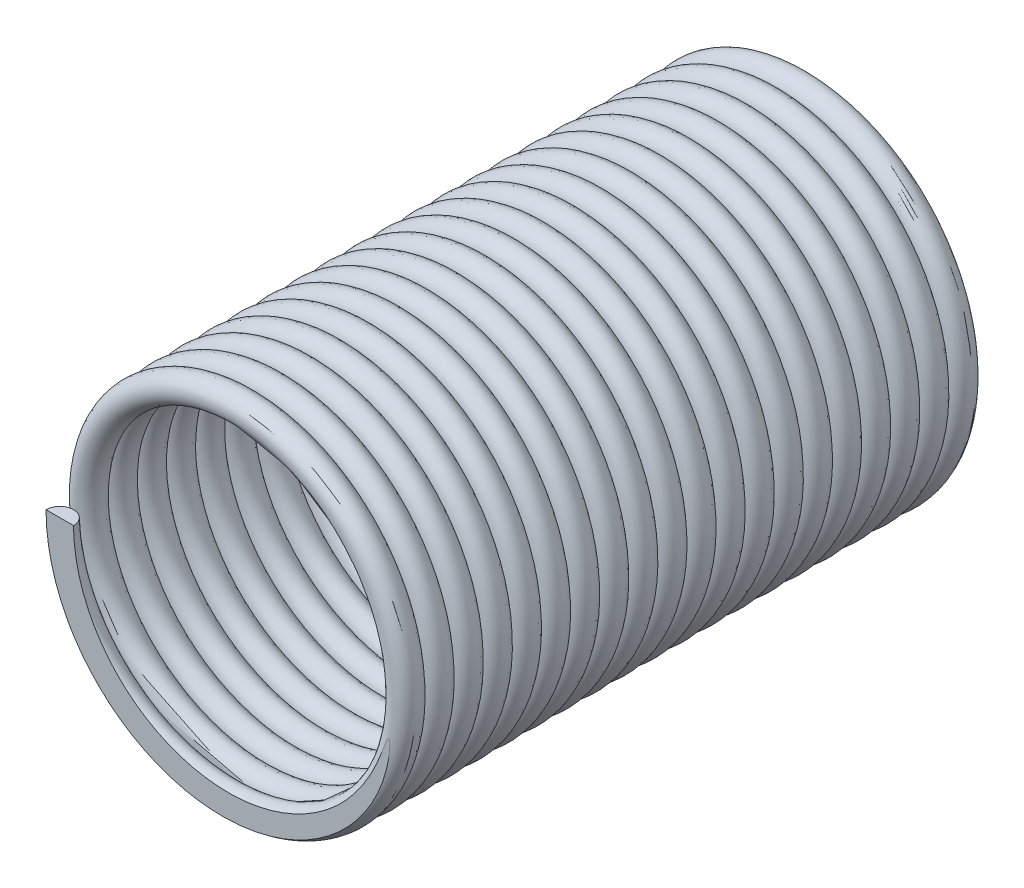
SolidWorks part; units mm, degrees
ref_plane "Front Plane" through (0, 0, 0) normal (0, 0, 1) x (1, 0, 0)
ref_plane "Top Plane" through (0, 0, 0) normal (0, 1, 0) x (1, 0, 0)
ref_plane "Right Plane" through (0, 0, 0) normal (1, 0, 0) x (0, 0, -1)
sketch "Sketch1" plane through (0, 0, 0) normal (0, 0, 1) x (1, 0, 0)
  circle A0 centre (0, 0) radius 14
sketch "Sketch3" plane through (0, 0, 0) normal (0, 0, 1) x (1, 0, 0)
  circle A0 centre (13, 0) radius 13
  point P4 (8.2777, 0)
sketch "Sketch4" plane through (0, 0, 0) normal (0, 0, 1) x (1, 0, 0)
  circle A0 centre (12, 0) radius 12
curve "Helix/Spiral3" pitch 2.1088 height 42.175 turns 20
sketch "Sketch7" plane through (0, 0, 0) normal (0, 1, 0) x (1, 0, 0)
  line L1 (12, 0) -> (12, -42.4605) construction
sketch "Sketch8" plane through (0, 0, 0) normal (0, 1, 0) x (1, 0, 0)
  circle A0 centre (0, 0) radius 1
  point P3 (4.8733, 5.5651)
sweep "Sweep4" add profiles "Sketch8" path "Helix/Spiral3"
ref_plane "Plane1" through (0, 0, -10) normal (0, 0, 1) x (1, 0, 0)
sketch "Sketch9" plane through (0, 0, -10) normal (0, 0, 1) x (1, 0, 0)
  line L1 (-1.3642, 14.2441) -> (25.4741, 14.2441)
  line L2 (-1.3642, 14.2441) -> (-1.3642, -14.2441)
  line L3 (-1.3642, -14.2441) -> (25.4741, -14.2441)
  line L4 (25.4741, 14.2441) -> (25.4741, -14.2441)
  line L5 (-1.3642, 14.2441) -> (25.4741, -14.2441) construction
  line L6 (-1.3642, -14.2441) -> (25.4741, 14.2441) construction
  point P0 (12.055, 0)
extrude "Cut-Extrude2" cut sketch "Sketch9" along normal blind 10
ref_plane "Plane2" through (0, 0, 52.175) normal (0, 0, 1) x (1, 0, 0)
sketch "Sketch10" plane through (0, 0, 52.175) normal (0, 0, 1) x (1, 0, 0)
  line L1 (27.234, 16.7189) -> (-3.124, 16.7189)
  line L2 (27.234, 16.7189) -> (27.234, -16.7189)
  line L3 (27.234, -16.7189) -> (-3.124, -16.7189)
  line L4 (-3.124, 16.7189) -> (-3.124, -16.7189)
  line L5 (27.234, 16.7189) -> (-3.124, -16.7189) construction
  line L6 (27.234, -16.7189) -> (-3.124, 16.7189) construction
  point P0 (12.055, 0)
extrude "Cut-Extrude3" cut sketch "Sketch10" against normal blind 10
